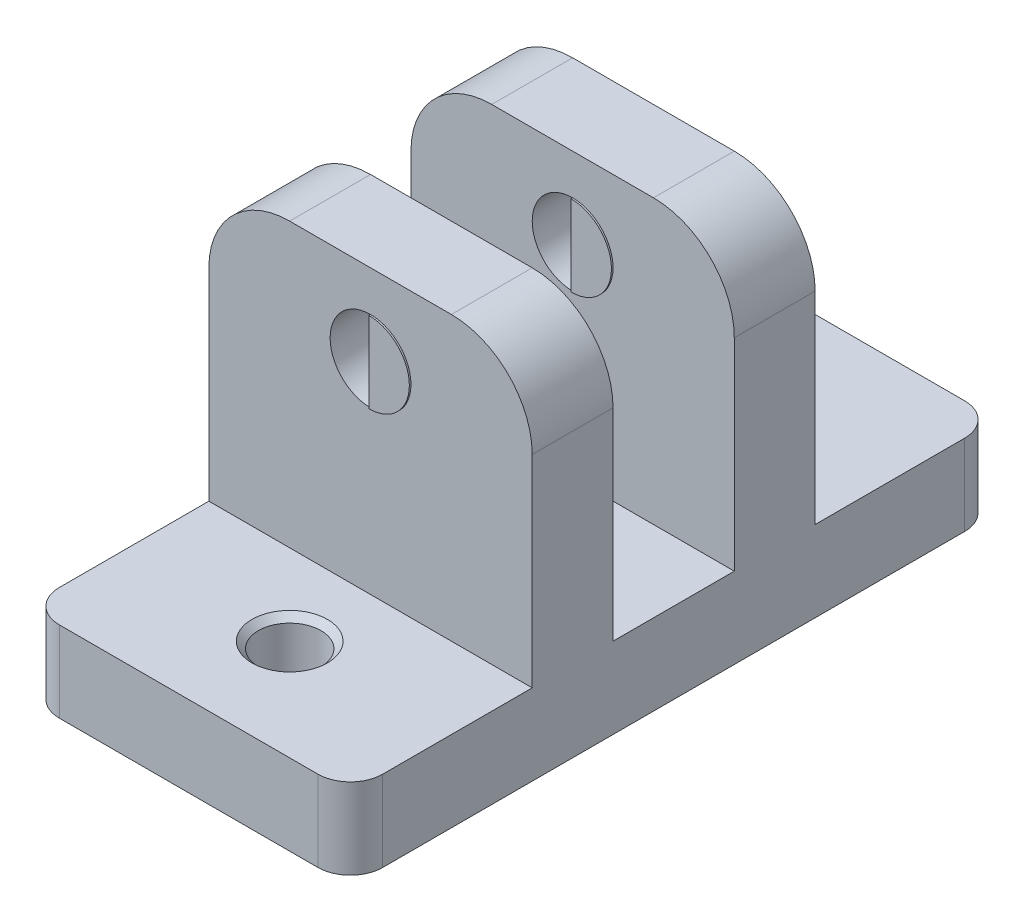
SolidWorks part; units mm, degrees
material "6061-T6 (SS)"
ref_plane "Front Plane" through (0, 0, 0) normal (0, 0, 1) x (1, 0, 0)
ref_plane "Top Plane" through (0, 0, 0) normal (0, 1, 0) x (1, 0, 0)
ref_plane "Right Plane" through (0, 0, 0) normal (1, 0, 0) x (0, 0, -1)
sketch "Sketch2" plane through (0, 0, 0) normal (0, 1, 0) x (1, 0, 0)
  line L1 (-12.7, -25.4) -> (12.7, -25.4)
  line L2 (-12.7, -25.4) -> (-12.7, 25.4)
  line L3 (-12.7, 25.4) -> (12.7, 25.4)
  line L4 (12.7, -25.4) -> (12.7, 25.4)
  line L5 (-12.7, -25.4) -> (12.7, 25.4) construction
  line L6 (-12.7, 25.4) -> (12.7, -25.4) construction
  point P0 (0, 0)
  dimension "D1" = 50.8
  dimension "D2" = 25.4
extrude "Boss-Extrude2" add sketch "Sketch2" along normal blind 28.575
sketch "Sketch3" plane through (12.7, 0, 0) normal (1, 0, 0) x (0, 0, -1)
  line L0 (-25.4, 28.575) -> (25.4, 28.575) construction
  line L1 (-25.4, 28.575) -> (-11.1125, 28.575)
  line L2 (-25.4, 28.575) -> (-25.4, 6.35)
  line L3 (-25.4, 6.35) -> (-11.1125, 6.35)
  line L4 (-11.1125, 28.575) -> (-11.1125, 6.35)
  line L5 (25.4, 28.575) -> (11.1125, 28.575)
  line L6 (25.4, 28.575) -> (25.4, 6.35)
  line L7 (25.4, 6.35) -> (11.1125, 6.35)
  line L8 (11.1125, 28.575) -> (11.1125, 6.35)
  line L9 (-4.7625, 28.575) -> (4.7625, 28.575)
  line L10 (-4.7625, 28.575) -> (-4.7625, 6.35)
  line L11 (-4.7625, 6.35) -> (4.7625, 6.35)
  line L12 (4.7625, 28.575) -> (4.7625, 6.35)
  line L13 (-25.4, 0) -> (25.4, 0) construction
  line L14 (0, 28.575) -> (0, 6.35) construction
  dimension "D1" = 6.35
  dimension "D2" = 6.35
  dimension "D3" = 9.525
extrude "Cut-Extrude1" cut sketch "Sketch3" against normal through all
sketch "Sketch5" plane through (0, 0, 25.4) normal (0, 0, 1) x (1, 0, 0)
  line L0 (-19.05, 28.575) -> (12.7, -9.525)
  line L5 (12.7, 6.35) -> (12.7, 28.575)
  line L6 (12.7, 28.575) -> (-12.7, 28.575)
  line L7 (-12.7, 28.575) -> (-12.7, 6.35)
  line L8 (-12.7, 6.35) -> (12.7, 6.35)
  line L9 (12.7, -9.525) -> (12.7, 28.575)
  line L10 (12.7, 28.575) -> (-19.05, 28.575)
  dimension "D2" = 31.75
  dimension "D3" = 38.1
  dimension "D1" = 0
hole_wizard "#10 (0.1935) Diameter Hole1" positions "Sketch6" profile "Sketch7" hole size "#10" standard "ANSI Inch"
sketch "Sketch6" plane through (0, 6.35, 0) normal (0, 1, 0) x (1, 0, 0)
  line L0 (0, -17.4625) -> (0, 17.4625) construction
  point P130 (0, -17.4625)
  point P132 (0, 17.4625)
  point P137 (0, 0)
  dimension "D1" = 34.925
sketch "Sketch7" plane through (0, 6.35, 17.4625) normal (1, 0, 0) x (0, 0, 1)
  line L0 (0, 0) -> (0, 7.8266)
  line L1 (0, 7.8266) -> (2.4574, 6.35)
  line L2 (2.4574, 6.35) -> (2.4574, 0)
  line L5 (2.4574, 0) -> (0, 0)
  line L10 (0, 7.8266) -> (-2.4575, 6.35) construction
  line L11 (0, -6.35) -> (0, 107.95) construction
  dimension "Hole Dia." = 4.9149
  dimension "Hole Depth" = 6.35
  dimension "Drill Angle" = 118
sketch "Sketch8" plane through (0, 0, -11.1125) normal (0, 0, -1) x (-1, 0, 0)
  line L1 (12.7, 28.575) -> (-12.7, 28.575) construction
  line L2 (0, 22.225) -> (0, 28.575) construction
  line L3 (12.7, 28.575) -> (-12.7, 28.575) construction
  circle A0 centre (0, 22.225) radius 3.175
  dimension "D1" = 6.35
  dimension "D3" = 6.35
extrude "Cut-Extrude3" cut sketch "Sketch8" against normal through all
ref_plane "Plane2" through (0, 0, 0) normal (0, 0, -1) x (-1, 0, 0)
fillet "Fillet1" radius 6.35 4 edges at (12.7, 28.575, 7.9375) (12.7, 28.575, -7.9375) (-12.7, 28.575, -7.9375) (-12.7, 28.575, 7.9375)
fillet "Fillet2" radius 2.54 4 edges at (12.7, 3.175, 25.4) (12.7, 3.175, -25.4) (-12.7, 3.175, 25.4) (-12.7, 3.175, -25.4)
chamfer "Chamfer1" distance 0.508 angle 45 4 edges at (0, 6.35, -15.005) (0, 0, -15.0051) (0, 6.35, 19.92) (0, 0, 19.92)
ref_plane "Plane3" through (0, 0, -7.9375) normal (0, 0, -1) x (-1, 0, 0)
sketch "Sketch10" plane through (0, 0, -7.9375) normal (0, 0, -1) x (-1, 0, 0)
  line L0 (0, 25.4) -> (0, 19.05)
  circle A0 centre (0, 22.225) radius 3.175 construction
  arc A1 (0, 25.4) -> (0, 19.05) centre (0, 22.225) ccw
extrude "Boss-Extrude3" add sketch "Sketch10" along normal blind 3.302 and the other way blind 3.302
mirror "Mirror1" about plane through (0, 0, 0) normal (0, 0, 1) of "Boss-Extrude3"
